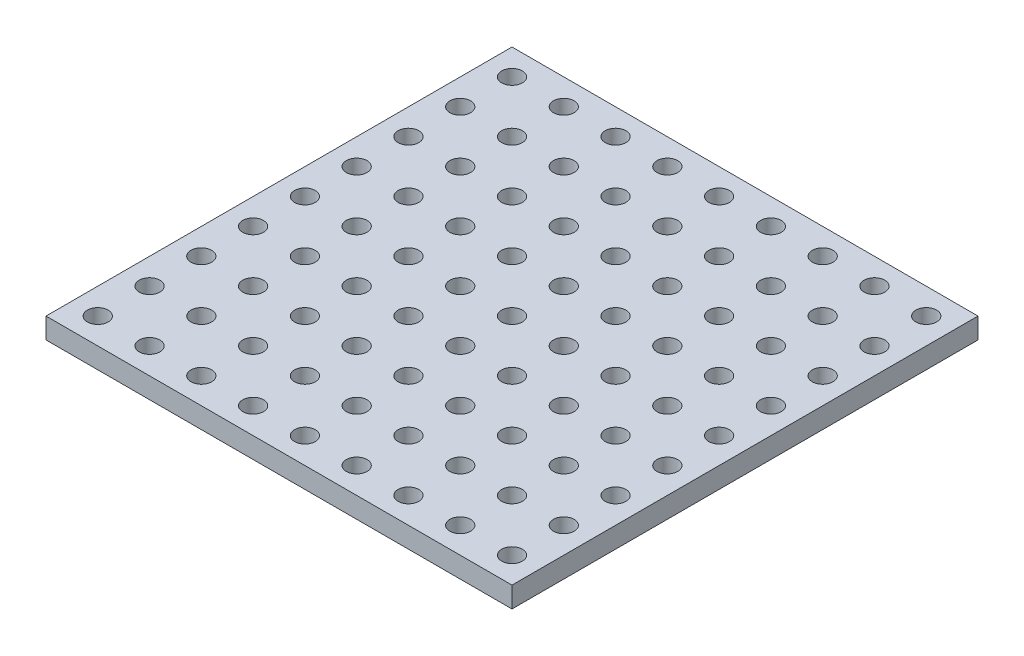
SolidWorks part; units mm, degrees
material "AISI 1020"
ref_plane "Plano frontal" through (0, 0, 0) normal (0, 0, 1) x (1, 0, 0)
ref_plane "Plano superior" through (0, 0, 0) normal (0, 1, 0) x (1, 0, 0)
ref_plane "Plano direito" through (0, 0, 0) normal (1, 0, 0) x (0, 0, -1)
sketch "Esboço1" plane through (0, 0, 0) normal (0, 1, 0) x (1, 0, 0)
  line L1 (-225, -225) -> (225, -225)
  line L2 (-225, -225) -> (-225, 225)
  line L3 (-225, 225) -> (225, 225)
  line L4 (225, -225) -> (225, 225)
  line L5 (-225, -225) -> (225, 225) construction
  line L6 (-225, 225) -> (225, -225) construction
  point P0 (0, 0)
  dimension "D1" = 450
extrude "Ressalto-extrusão1" add sketch "Esboço1" along normal blind 20
sketch "Esboço2" plane through (0, 20, 0) normal (0, 1, 0) x (1, 0, 0)
  line L0 (-225, 225) -> (-225, -225) construction
  line L1 (225, 225) -> (-225, 225) construction
  circle A0 centre (-200, 200) radius 10
  circle A1 centre (-150, 200) radius 10
  circle A2 centre (-100, 200) radius 10
  circle A3 centre (-50, 200) radius 10
  circle A4 centre (0, 200) radius 10
  circle A5 centre (50, 200) radius 10
  circle A6 centre (100, 200) radius 10
  circle A7 centre (150, 200) radius 10
  circle A8 centre (200, 200) radius 10
  circle A9 centre (250, 200) radius 10
  circle A10 centre (-150, 150) radius 10
  circle A11 centre (-100, 150) radius 10
  circle A12 centre (-50, 150) radius 10
  circle A13 centre (0, 150) radius 10
  circle A14 centre (50, 150) radius 10
  circle A15 centre (100, 150) radius 10
  circle A16 centre (150, 150) radius 10
  circle A17 centre (200, 150) radius 10
  circle A18 centre (250, 150) radius 10
  circle A19 centre (-150, 100) radius 10
  circle A20 centre (-100, 100) radius 10
  circle A21 centre (-50, 100) radius 10
  circle A22 centre (0, 100) radius 10
  circle A23 centre (50, 100) radius 10
  circle A24 centre (100, 100) radius 10
  circle A25 centre (150, 100) radius 10
  circle A26 centre (200, 100) radius 10
  circle A27 centre (250, 100) radius 10
  circle A28 centre (-150, 50) radius 10
  circle A29 centre (-100, 50) radius 10
  circle A30 centre (-50, 50) radius 10
  circle A31 centre (0, 50) radius 10
  circle A32 centre (50, 50) radius 10
  circle A33 centre (100, 50) radius 10
  circle A34 centre (150, 50) radius 10
  circle A35 centre (200, 50) radius 10
  circle A36 centre (250, 50) radius 10
  circle A37 centre (-150, 0) radius 10
  circle A38 centre (-100, 0) radius 10
  circle A39 centre (-50, 0) radius 10
  circle A40 centre (0, 0) radius 10
  circle A41 centre (50, 0) radius 10
  circle A42 centre (100, 0) radius 10
  circle A43 centre (150, 0) radius 10
  circle A44 centre (200, 0) radius 10
  circle A45 centre (250, 0) radius 10
  circle A46 centre (-150, -50) radius 10
  circle A47 centre (-100, -50) radius 10
  circle A48 centre (-50, -50) radius 10
  circle A49 centre (0, -50) radius 10
  circle A50 centre (50, -50) radius 10
  circle A51 centre (100, -50) radius 10
  circle A52 centre (150, -50) radius 10
  circle A53 centre (200, -50) radius 10
  circle A54 centre (250, -50) radius 10
  circle A55 centre (-150, -100) radius 10
  circle A56 centre (-100, -100) radius 10
  circle A57 centre (-50, -100) radius 10
  circle A58 centre (0, -100) radius 10
  circle A59 centre (50, -100) radius 10
  circle A60 centre (100, -100) radius 10
  circle A61 centre (150, -100) radius 10
  circle A62 centre (200, -100) radius 10
  circle A63 centre (250, -100) radius 10
  circle A64 centre (-150, -150) radius 10
  circle A65 centre (-100, -150) radius 10
  circle A66 centre (-50, -150) radius 10
  circle A67 centre (0, -150) radius 10
  circle A68 centre (50, -150) radius 10
  circle A69 centre (100, -150) radius 10
  circle A70 centre (150, -150) radius 10
  circle A71 centre (200, -150) radius 10
  circle A72 centre (250, -150) radius 10
  circle A73 centre (-150, -200) radius 10
  circle A74 centre (-100, -200) radius 10
  circle A75 centre (-50, -200) radius 10
  circle A76 centre (0, -200) radius 10
  circle A77 centre (50, -200) radius 10
  circle A78 centre (100, -200) radius 10
  circle A79 centre (150, -200) radius 10
  circle A80 centre (200, -200) radius 10
  circle A81 centre (250, -200) radius 10
  circle A82 centre (-150, -250) radius 10
  circle A83 centre (-100, -250) radius 10
  circle A84 centre (-50, -250) radius 10
  circle A85 centre (0, -250) radius 10
  circle A86 centre (50, -250) radius 10
  circle A87 centre (100, -250) radius 10
  circle A88 centre (150, -250) radius 10
  circle A89 centre (200, -250) radius 10
  circle A90 centre (250, -250) radius 10
  circle A91 centre (-200, 150) radius 10
  circle A92 centre (-200, 100) radius 10
  circle A93 centre (-200, 50) radius 10
  circle A94 centre (-200, 0) radius 10
  circle A95 centre (-200, -50) radius 10
  circle A96 centre (-200, -100) radius 10
  circle A97 centre (-200, -150) radius 10
  circle A98 centre (-200, -200) radius 10
  circle A99 centre (-200, -250) radius 10
  dimension "D1" = 20
  dimension "D2" = 25
  dimension "D3" = 25
  dimension "D4" = 10
  dimension "D5" = 10
extrude "Corte-extrusão1" cut sketch "Esboço2" against normal through all
